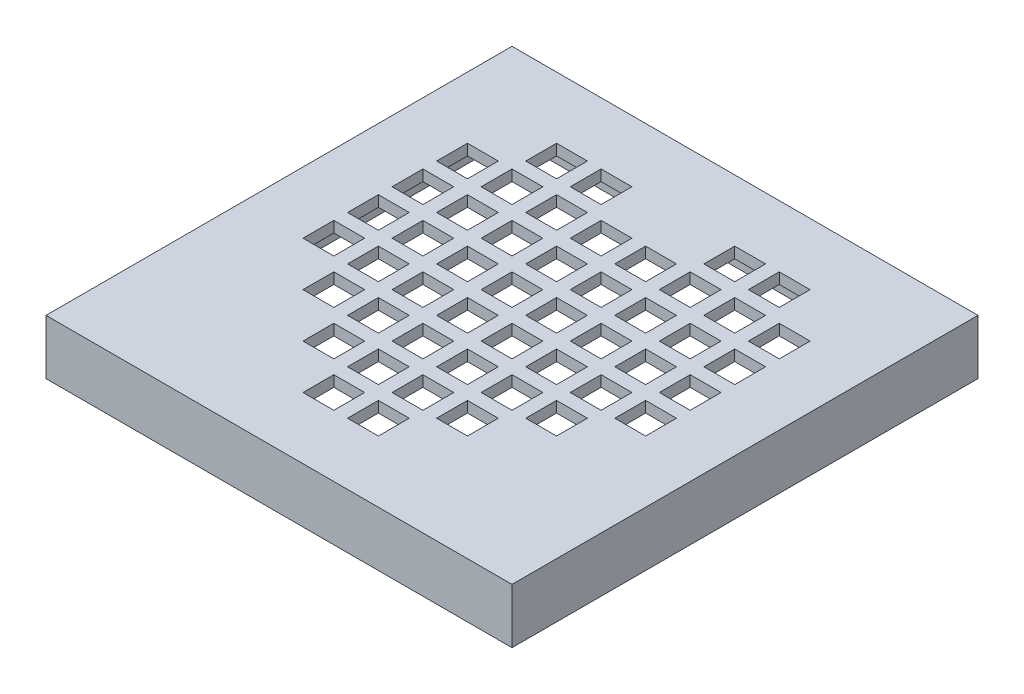
SolidWorks part; units mm, degrees
ref_plane "Front Plane" through (0, 0, 0) normal (0, 0, 1) x (1, 0, 0)
ref_plane "Top Plane" through (0, 0, 0) normal (0, 1, 0) x (1, 0, 0)
ref_plane "Right Plane" through (0, 0, 0) normal (1, 0, 0) x (0, 0, -1)
sketch "Sketch1" plane through (0, 0, 0) normal (0, 1, 0) x (1, 0, 0)
  line L1 (-8.5, -8.5) -> (8.5, -8.5)
  line L2 (-8.5, -8.5) -> (-8.5, 8.5)
  line L3 (-8.5, 8.5) -> (8.5, 8.5)
  line L4 (8.5, -8.5) -> (8.5, 8.5)
  line L5 (-8.5, -8.5) -> (8.5, 8.5) construction
  line L6 (-8.5, 8.5) -> (8.5, -8.5) construction
  point P0 (0, 0)
  dimension "D1" = 17
extrude "Boss-Extrude1" add sketch "Sketch1" along normal blind 2
sketch "Sketch2" plane through (0, 0, 0) normal (0, -1, 0) x (1, 0, 0)
  line L1 (-7.6, -7.6) -> (7.6, -7.6)
  line L2 (-7.6, -7.6) -> (-7.6, 7.6)
  line L3 (-7.6, 7.6) -> (7.6, 7.6)
  line L4 (7.6, -7.6) -> (7.6, 7.6)
  line L5 (-7.6, -7.6) -> (7.6, 7.6) construction
  line L6 (-7.6, 7.6) -> (7.6, -7.6) construction
  point P0 (0, 0)
  dimension "D1" = 15.2
extrude "Cut-Extrude1" cut sketch "Sketch2" against normal blind 1.6
sketch "Sketch3" plane through (0, 2, 0) normal (0, 1, 0) x (1, 0, 0)
  line L0 (-6.5, -4.875) -> (-4.875, -6.5) construction
  line L1 (-6.5, -6.5) -> (6.5, -6.5) construction
  line L2 (-6.5, -6.5) -> (-6.5, 6.5) construction
  line L3 (-6.5, 6.5) -> (6.5, 6.5) construction
  line L4 (6.5, -6.5) -> (6.5, 6.5) construction
  line L5 (-6.5, -6.5) -> (6.5, 6.5) construction
  line L6 (-6.5, 6.5) -> (6.5, -6.5) construction
  line L7 (-6.5, -6.5) -> (-4.875, -6.5) construction
  line L8 (-6.5, -6.5) -> (-6.5, -4.875) construction
  line L9 (-6.5, -4.875) -> (-4.875, -4.875) construction
  line L10 (-4.875, -6.5) -> (-4.875, -4.875) construction
  line L11 (-4.625, -5.125) -> (-3.5, -5.125)
  line L12 (-6.25, -6.25) -> (-5.125, -6.25)
  line L13 (-6.25, -6.25) -> (-6.25, -5.125)
  line L14 (-6.25, -5.125) -> (-5.125, -5.125)
  line L15 (-5.125, -6.25) -> (-5.125, -5.125)
  line L16 (-6.25, -6.25) -> (-5.125, -5.125) construction
  line L17 (-6.25, -5.125) -> (-5.125, -6.25) construction
  line L18 (-4.625, -6.25) -> (-4.625, -5.125)
  line L19 (-4.625, -6.25) -> (-3.5, -6.25)
  line L20 (-3.5, -6.25) -> (-3.5, -5.125)
  line L21 (-3, -5.125) -> (-1.875, -5.125)
  line L22 (-3, -6.25) -> (-3, -5.125)
  line L23 (-3, -6.25) -> (-1.875, -6.25)
  line L24 (-1.875, -6.25) -> (-1.875, -5.125)
  line L25 (-1.375, -5.125) -> (-0.25, -5.125)
  line L26 (-1.375, -6.25) -> (-1.375, -5.125)
  line L27 (-1.375, -6.25) -> (-0.25, -6.25)
  line L28 (-0.25, -6.25) -> (-0.25, -5.125)
  line L29 (0.25, -5.125) -> (1.375, -5.125)
  line L30 (0.25, -6.25) -> (0.25, -5.125)
  line L31 (0.25, -6.25) -> (1.375, -6.25)
  line L32 (1.375, -6.25) -> (1.375, -5.125)
  line L33 (1.875, -5.125) -> (3, -5.125)
  line L34 (1.875, -6.25) -> (1.875, -5.125)
  line L35 (1.875, -6.25) -> (3, -6.25)
  line L36 (3, -6.25) -> (3, -5.125)
  line L37 (3.5, -5.125) -> (4.625, -5.125)
  line L38 (3.5, -6.25) -> (3.5, -5.125)
  line L39 (3.5, -6.25) -> (4.625, -6.25)
  line L40 (4.625, -6.25) -> (4.625, -5.125)
  line L41 (5.125, -5.125) -> (6.25, -5.125)
  line L42 (5.125, -6.25) -> (5.125, -5.125)
  line L43 (5.125, -6.25) -> (6.25, -6.25)
  line L44 (6.25, -6.25) -> (6.25, -5.125)
  line L53 (-4.625, -3.5) -> (-3.5, -3.5)
  line L54 (-4.625, -4.625) -> (-4.625, -3.5)
  line L55 (-4.625, -4.625) -> (-3.5, -4.625)
  line L56 (-3.5, -4.625) -> (-3.5, -3.5)
  line L57 (-3, -3.5) -> (-1.875, -3.5)
  line L58 (-3, -4.625) -> (-3, -3.5)
  line L59 (-3, -4.625) -> (-1.875, -4.625)
  line L60 (-1.875, -4.625) -> (-1.875, -3.5)
  line L61 (-1.375, -3.5) -> (-0.25, -3.5)
  line L62 (-1.375, -4.625) -> (-1.375, -3.5)
  line L63 (-1.375, -4.625) -> (-0.25, -4.625)
  line L64 (-0.25, -4.625) -> (-0.25, -3.5)
  line L65 (0.25, -3.5) -> (1.375, -3.5)
  line L66 (0.25, -4.625) -> (0.25, -3.5)
  line L67 (0.25, -4.625) -> (1.375, -4.625)
  line L68 (1.375, -4.625) -> (1.375, -3.5)
  line L69 (1.875, -3.5) -> (3, -3.5)
  line L70 (1.875, -4.625) -> (1.875, -3.5)
  line L71 (1.875, -4.625) -> (3, -4.625)
  line L72 (3, -4.625) -> (3, -3.5)
  line L73 (3.5, -3.5) -> (4.625, -3.5)
  line L74 (3.5, -4.625) -> (3.5, -3.5)
  line L75 (3.5, -4.625) -> (4.625, -4.625)
  line L76 (4.625, -4.625) -> (4.625, -3.5)
  line L77 (5.125, -3.5) -> (6.25, -3.5)
  line L78 (5.125, -4.625) -> (5.125, -3.5)
  line L79 (5.125, -4.625) -> (6.25, -4.625)
  line L80 (6.25, -4.625) -> (6.25, -3.5)
  line L89 (-4.625, -1.875) -> (-3.5, -1.875)
  line L90 (-4.625, -3) -> (-4.625, -1.875)
  line L91 (-4.625, -3) -> (-3.5, -3)
  line L92 (-3.5, -3) -> (-3.5, -1.875)
  line L93 (-3, -1.875) -> (-1.875, -1.875)
  line L94 (-3, -3) -> (-3, -1.875)
  line L95 (-3, -3) -> (-1.875, -3)
  line L96 (-1.875, -3) -> (-1.875, -1.875)
  line L97 (-1.375, -1.875) -> (-0.25, -1.875)
  line L98 (-1.375, -3) -> (-1.375, -1.875)
  line L99 (-1.375, -3) -> (-0.25, -3)
  line L100 (-0.25, -3) -> (-0.25, -1.875)
  line L101 (0.25, -1.875) -> (1.375, -1.875)
  line L102 (0.25, -3) -> (0.25, -1.875)
  line L103 (0.25, -3) -> (1.375, -3)
  line L104 (1.375, -3) -> (1.375, -1.875)
  line L105 (1.875, -1.875) -> (3, -1.875)
  line L106 (1.875, -3) -> (1.875, -1.875)
  line L107 (1.875, -3) -> (3, -3)
  line L108 (3, -3) -> (3, -1.875)
  line L109 (3.5, -1.875) -> (4.625, -1.875)
  line L110 (3.5, -3) -> (3.5, -1.875)
  line L111 (3.5, -3) -> (4.625, -3)
  line L112 (4.625, -3) -> (4.625, -1.875)
  line L113 (5.125, -1.875) -> (6.25, -1.875)
  line L114 (5.125, -3) -> (5.125, -1.875)
  line L115 (5.125, -3) -> (6.25, -3)
  line L116 (6.25, -3) -> (6.25, -1.875)
  line L125 (-4.625, -0.25) -> (-3.5, -0.25)
  line L126 (-4.625, -1.375) -> (-4.625, -0.25)
  line L127 (-4.625, -1.375) -> (-3.5, -1.375)
  line L128 (-3.5, -1.375) -> (-3.5, -0.25)
  line L129 (-3, -0.25) -> (-1.875, -0.25)
  line L130 (-3, -1.375) -> (-3, -0.25)
  line L131 (-3, -1.375) -> (-1.875, -1.375)
  line L132 (-1.875, -1.375) -> (-1.875, -0.25)
  line L133 (-1.375, -0.25) -> (-0.25, -0.25)
  line L134 (-1.375, -1.375) -> (-1.375, -0.25)
  line L135 (-1.375, -1.375) -> (-0.25, -1.375)
  line L136 (-0.25, -1.375) -> (-0.25, -0.25)
  line L137 (0.25, -0.25) -> (1.375, -0.25)
  line L138 (0.25, -1.375) -> (0.25, -0.25)
  line L139 (0.25, -1.375) -> (1.375, -1.375)
  line L140 (1.375, -1.375) -> (1.375, -0.25)
  line L141 (1.875, -0.25) -> (3, -0.25)
  line L142 (1.875, -1.375) -> (1.875, -0.25)
  line L143 (1.875, -1.375) -> (3, -1.375)
  line L144 (3, -1.375) -> (3, -0.25)
  line L145 (3.5, -0.25) -> (4.625, -0.25)
  line L146 (3.5, -1.375) -> (3.5, -0.25)
  line L147 (3.5, -1.375) -> (4.625, -1.375)
  line L148 (4.625, -1.375) -> (4.625, -0.25)
  line L149 (5.125, -0.25) -> (6.25, -0.25)
  line L150 (5.125, -1.375) -> (5.125, -0.25)
  line L151 (5.125, -1.375) -> (6.25, -1.375)
  line L152 (6.25, -1.375) -> (6.25, -0.25)
  line L161 (-4.625, 1.375) -> (-3.5, 1.375)
  line L162 (-4.625, 0.25) -> (-4.625, 1.375)
  line L163 (-4.625, 0.25) -> (-3.5, 0.25)
  line L164 (-3.5, 0.25) -> (-3.5, 1.375)
  line L165 (-3, 1.375) -> (-1.875, 1.375)
  line L166 (-3, 0.25) -> (-3, 1.375)
  line L167 (-3, 0.25) -> (-1.875, 0.25)
  line L168 (-1.875, 0.25) -> (-1.875, 1.375)
  line L169 (-1.375, 1.375) -> (-0.25, 1.375)
  line L170 (-1.375, 0.25) -> (-1.375, 1.375)
  line L171 (-1.375, 0.25) -> (-0.25, 0.25)
  line L172 (-0.25, 0.25) -> (-0.25, 1.375)
  line L173 (0.25, 1.375) -> (1.375, 1.375)
  line L174 (0.25, 0.25) -> (0.25, 1.375)
  line L175 (0.25, 0.25) -> (1.375, 0.25)
  line L176 (1.375, 0.25) -> (1.375, 1.375)
  line L177 (1.875, 1.375) -> (3, 1.375)
  line L178 (1.875, 0.25) -> (1.875, 1.375)
  line L179 (1.875, 0.25) -> (3, 0.25)
  line L180 (3, 0.25) -> (3, 1.375)
  line L181 (3.5, 1.375) -> (4.625, 1.375)
  line L182 (3.5, 0.25) -> (3.5, 1.375)
  line L183 (3.5, 0.25) -> (4.625, 0.25)
  line L184 (4.625, 0.25) -> (4.625, 1.375)
  line L185 (5.125, 1.375) -> (6.25, 1.375)
  line L186 (5.125, 0.25) -> (5.125, 1.375)
  line L187 (5.125, 0.25) -> (6.25, 0.25)
  line L188 (6.25, 0.25) -> (6.25, 1.375)
  line L197 (-4.625, 3) -> (-3.5, 3)
  line L198 (-4.625, 1.875) -> (-4.625, 3)
  line L199 (-4.625, 1.875) -> (-3.5, 1.875)
  line L200 (-3.5, 1.875) -> (-3.5, 3)
  line L201 (-3, 3) -> (-1.875, 3)
  line L202 (-3, 1.875) -> (-3, 3)
  line L203 (-3, 1.875) -> (-1.875, 1.875)
  line L204 (-1.875, 1.875) -> (-1.875, 3)
  line L205 (-1.375, 3) -> (-0.25, 3)
  line L206 (-1.375, 1.875) -> (-1.375, 3)
  line L207 (-1.375, 1.875) -> (-0.25, 1.875)
  line L208 (-0.25, 1.875) -> (-0.25, 3)
  line L209 (0.25, 3) -> (1.375, 3)
  line L210 (0.25, 1.875) -> (0.25, 3)
  line L211 (0.25, 1.875) -> (1.375, 1.875)
  line L212 (1.375, 1.875) -> (1.375, 3)
  line L213 (1.875, 3) -> (3, 3)
  line L214 (1.875, 1.875) -> (1.875, 3)
  line L215 (1.875, 1.875) -> (3, 1.875)
  line L216 (3, 1.875) -> (3, 3)
  line L217 (3.5, 3) -> (4.625, 3)
  line L218 (3.5, 1.875) -> (3.5, 3)
  line L219 (3.5, 1.875) -> (4.625, 1.875)
  line L220 (4.625, 1.875) -> (4.625, 3)
  line L221 (5.125, 3) -> (6.25, 3)
  line L222 (5.125, 1.875) -> (5.125, 3)
  line L223 (5.125, 1.875) -> (6.25, 1.875)
  line L224 (6.25, 1.875) -> (6.25, 3)
  line L233 (-4.625, 4.625) -> (-3.5, 4.625)
  line L234 (-4.625, 3.5) -> (-4.625, 4.625)
  line L235 (-4.625, 3.5) -> (-3.5, 3.5)
  line L236 (-3.5, 3.5) -> (-3.5, 4.625)
  line L237 (-3, 4.625) -> (-1.875, 4.625)
  line L238 (-3, 3.5) -> (-3, 4.625)
  line L239 (-3, 3.5) -> (-1.875, 3.5)
  line L240 (-1.875, 3.5) -> (-1.875, 4.625)
  line L241 (-1.375, 4.625) -> (-0.25, 4.625)
  line L242 (-1.375, 3.5) -> (-1.375, 4.625)
  line L243 (-1.375, 3.5) -> (-0.25, 3.5)
  line L244 (-0.25, 3.5) -> (-0.25, 4.625)
  line L245 (0.25, 4.625) -> (1.375, 4.625)
  line L246 (0.25, 3.5) -> (0.25, 4.625)
  line L247 (0.25, 3.5) -> (1.375, 3.5)
  line L248 (1.375, 3.5) -> (1.375, 4.625)
  line L249 (1.875, 4.625) -> (3, 4.625)
  line L250 (1.875, 3.5) -> (1.875, 4.625)
  line L251 (1.875, 3.5) -> (3, 3.5)
  line L252 (3, 3.5) -> (3, 4.625)
  line L253 (3.5, 4.625) -> (4.625, 4.625)
  line L254 (3.5, 3.5) -> (3.5, 4.625)
  line L255 (3.5, 3.5) -> (4.625, 3.5)
  line L256 (4.625, 3.5) -> (4.625, 4.625)
  line L257 (5.125, 4.625) -> (6.25, 4.625)
  line L258 (5.125, 3.5) -> (5.125, 4.625)
  line L259 (5.125, 3.5) -> (6.25, 3.5)
  line L260 (6.25, 3.5) -> (6.25, 4.625)
  line L269 (-4.625, 6.25) -> (-3.5, 6.25)
  line L270 (-4.625, 5.125) -> (-4.625, 6.25)
  line L271 (-4.625, 5.125) -> (-3.5, 5.125)
  line L272 (-3.5, 5.125) -> (-3.5, 6.25)
  line L273 (-3, 6.25) -> (-1.875, 6.25)
  line L274 (-3, 5.125) -> (-3, 6.25)
  line L275 (-3, 5.125) -> (-1.875, 5.125)
  line L276 (-1.875, 5.125) -> (-1.875, 6.25)
  line L277 (-1.375, 6.25) -> (-0.25, 6.25)
  line L278 (-1.375, 5.125) -> (-1.375, 6.25)
  line L279 (-1.375, 5.125) -> (-0.25, 5.125)
  line L280 (-0.25, 5.125) -> (-0.25, 6.25)
  line L281 (0.25, 6.25) -> (1.375, 6.25)
  line L282 (0.25, 5.125) -> (0.25, 6.25)
  line L283 (0.25, 5.125) -> (1.375, 5.125)
  line L284 (1.375, 5.125) -> (1.375, 6.25)
  line L285 (1.875, 6.25) -> (3, 6.25)
  line L286 (1.875, 5.125) -> (1.875, 6.25)
  line L287 (1.875, 5.125) -> (3, 5.125)
  line L288 (3, 5.125) -> (3, 6.25)
  line L289 (3.5, 6.25) -> (4.625, 6.25)
  line L290 (3.5, 5.125) -> (3.5, 6.25)
  line L291 (3.5, 5.125) -> (4.625, 5.125)
  line L292 (4.625, 5.125) -> (4.625, 6.25)
  line L293 (5.125, 6.25) -> (6.25, 6.25)
  line L294 (5.125, 5.125) -> (5.125, 6.25)
  line L295 (5.125, 5.125) -> (6.25, 5.125)
  line L296 (6.25, 5.125) -> (6.25, 6.25)
  line L377 (-6.25, -3.5) -> (-5.125, -3.5)
  line L378 (-6.25, -4.625) -> (-6.25, -3.5)
  line L379 (-6.25, -4.625) -> (-5.125, -4.625)
  line L380 (-5.125, -4.625) -> (-5.125, -3.5)
  line L381 (-6.25, -1.875) -> (-5.125, -1.875)
  line L382 (-6.25, -3) -> (-6.25, -1.875)
  line L383 (-6.25, -3) -> (-5.125, -3)
  line L384 (-5.125, -3) -> (-5.125, -1.875)
  line L385 (-6.25, -0.25) -> (-5.125, -0.25)
  line L386 (-6.25, -1.375) -> (-6.25, -0.25)
  line L387 (-6.25, -1.375) -> (-5.125, -1.375)
  line L388 (-5.125, -1.375) -> (-5.125, -0.25)
  line L389 (-6.25, 1.375) -> (-5.125, 1.375)
  line L390 (-6.25, 0.25) -> (-6.25, 1.375)
  line L391 (-6.25, 0.25) -> (-5.125, 0.25)
  line L392 (-5.125, 0.25) -> (-5.125, 1.375)
  line L393 (-6.25, 3) -> (-5.125, 3)
  line L394 (-6.25, 1.875) -> (-6.25, 3)
  line L395 (-6.25, 1.875) -> (-5.125, 1.875)
  line L396 (-5.125, 1.875) -> (-5.125, 3)
  line L397 (-6.25, 4.625) -> (-5.125, 4.625)
  line L398 (-6.25, 3.5) -> (-6.25, 4.625)
  line L399 (-6.25, 3.5) -> (-5.125, 3.5)
  line L400 (-5.125, 3.5) -> (-5.125, 4.625)
  line L401 (-6.25, 6.25) -> (-5.125, 6.25)
  line L402 (-6.25, 5.125) -> (-6.25, 6.25)
  line L403 (-6.25, 5.125) -> (-5.125, 5.125)
  line L404 (-5.125, 5.125) -> (-5.125, 6.25)
  point P0 (0, 0)
  point P9 (-5.6875, -5.6875)
  point P14 (-5.6875, -5.125)
  dimension "D1" = 13
  dimension "D2" = 1.625
  dimension "D3" = 0.25
  dimension "D4" = 8
  dimension "D5" = 8
extrude "Cut-Extrude2" cut sketch "Sketch3" against normal through all contours L271 L272 L269 L270 | L275 L276 L273 L274 | L287 L288 L285 L286 | L291 L292 L289 L290 | L259 L260 L257 L258 | L223 L224 L221 L222 | L187 L188 L185 L186 | L399 L400 L397 L398 | L395 L396 L393 L394 | L391 L392 L389 L390 | L127 L128 L125 L126 | L95 L96 L93 L94 | L63 L64 L61 L62 | L67 L68 L65 L66 | L107 L108 L105 L106 | L147 L148 L145 L146 | L243 L244 L241 L242 | L247 L248 L245 L246 | L235 L236 L233 L234 | L199 L200 L197 L198 | L167 L168 L165 L166 | L203 L204 L201 L202 | L239 L240 L237 L238 | L207 L208 L205 L206 | L211 L212 L209 L210 | L179 L180 L177 L178 | L215 L216 L213 L214 | L251 L252 L249 L250 | L219 L220 L217 L218 | L183 L184 L181 L182 | L143 L144 L141 L142 | L139 L140 L137 L138 | L131 L132 L129 L130 | L99 L100 L97 L98 | L103 L104 L101 L102 | L135 L136 L133 L134 | L163 L164 L161 L162 | L171 L172 L169 L170 | L175 L176 L173 L174 | L255 L256 L253 L254 | L151 L152 L149 L150 | L111 L112 L109 L110 | L71 L72 L69 L70 | L31 L32 L29 L30 | L27 L28 L25 L26 | L59 L60 L57 L58 | L91 L92 L89 L90 | L387 L388 L385 L386
